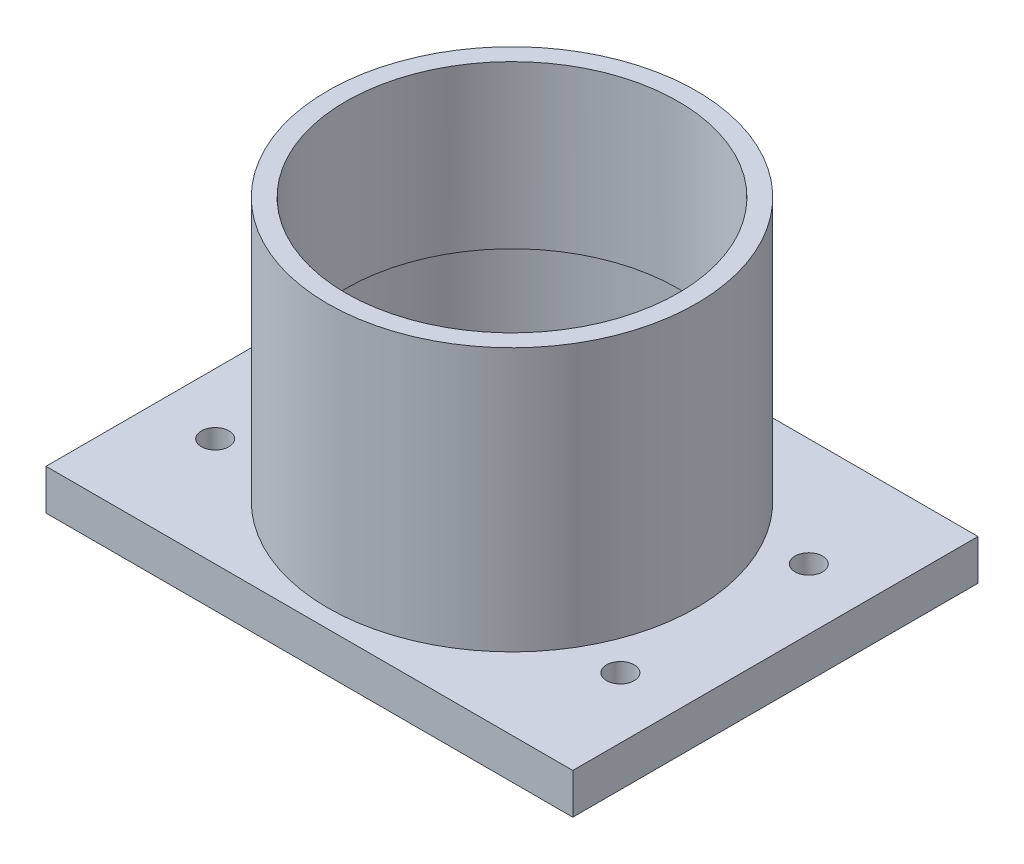
SolidWorks part; units mm, degrees
ref_plane "Front Plane" through (0, 0, 0) normal (0, 0, 1) x (1, 0, 0)
ref_plane "Top Plane" through (0, 0, 0) normal (0, 1, 0) x (1, 0, 0)
ref_plane "Right Plane" through (0, 0, 0) normal (1, 0, 0) x (0, 0, -1)
sketch "Sketch1" plane through (0, 0, 0) normal (0, 1, 0) x (1, 0, 0)
  line L1 (-65, -50) -> (65, -50)
  line L2 (-65, -50) -> (-65, 50)
  line L3 (-65, 50) -> (65, 50)
  line L4 (65, -50) -> (65, 50)
  line L5 (-65, -50) -> (65, 50) construction
  line L6 (-65, 50) -> (65, -50) construction
  point P0 (0, 0)
  dimension "D1" = 130
  dimension "D2" = 100
extrude "Boss-Extrude1" add sketch "Sketch1" along normal blind 10
sketch "Sketch2" plane through (0, 10, 0) normal (0, 1, 0) x (1, 0, 0)
  circle A0 centre (0, 0) radius 45.5
  dimension "D1" = 91
extrude "Boss-Extrude2" add sketch "Sketch2" along normal blind 65
sketch "Sketch3" plane through (0, 75, 0) normal (0, 1, 0) x (1, 0, 0)
  circle A0 centre (0, 0) radius 41
  dimension "D1" = 82
extrude "Cut-Extrude1" cut sketch "Sketch3" against normal through all
sketch "Sketch4" plane through (0, 0, 0) normal (0, -1, 0) x (1, 0, 0)
  circle A0 centre (0, 0) radius 42.5
  dimension "D1" = 85
extrude "Cut-Extrude2" cut sketch "Sketch4" against normal blind 35
sketch "Sketch8" plane through (0, 10, 0) normal (0, 1, 0) x (1, 0, 0)
  line L0 (-50, 23.25) -> (50, 23.25) construction
  line L1 (50, 23.25) -> (50, -23.25) construction
  point P0 (-50, 23.25)
  point P1 (-50, -23.25)
  point P2 (50, 23.25)
  point P3 (50, -23.25)
  point P9 (0, 23.25)
  point P11 (50, 0)
  dimension "D1" = 100
  dimension "D2" = 46.5
hole_wizard "M8 Tapped Hole1" positions "Sketch9" profile "Sketch10" tap size "M8" standard "ISO"
sketch "Sketch9" plane through (0, 10, 0) normal (0, 1, 0) x (1, 0, 0)
  point P0 (-50, 23.25)
  point P3 (-50, -23.25)
  point P6 (50, -23.25)
  point P9 (50, 23.25)
sketch "Sketch10" plane through (-50, 10, -23.25) normal (1, 0, 0) x (0, 0, 1)
  line L0 (0, 0) -> (0, 19.75)
  line L1 (0, 19.75) -> (3.4, 17.7071)
  line L2 (3.4, 17.7071) -> (3.4, 0)
  line L5 (3.4, 0) -> (0, 0)
  line L10 (0, 19.75) -> (-3.4, 17.7071) construction
  line L11 (0, -6.35) -> (0, 107.95) construction
  dimension "Tap Drill Dia." = 6.8
  dimension "Tap Drill Depth" = 19.75
  dimension "Drill Angle" = 118
cosmetic thread "Hole Thread1"
cosmetic thread "Hole Thread2"
cosmetic thread "Hole Thread3"
cosmetic thread "Hole Thread4"
